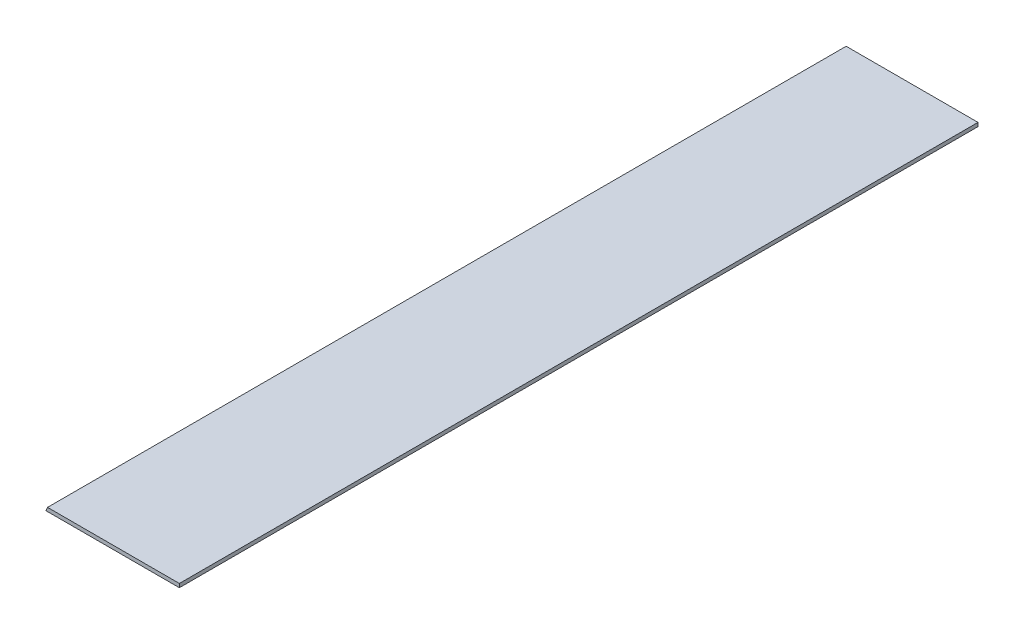
SolidWorks part; units mm, degrees
ref_plane "Front Plane" through (0, 0, 0) normal (0, 0, 1) x (1, 0, 0)
ref_plane "Top Plane" through (0, 0, 0) normal (0, 1, 0) x (1, 0, 0)
ref_plane "Right Plane" through (0, 0, 0) normal (1, 0, 0) x (0, 0, -1)
sketch "Sketch1" plane through (0, 0, 0) normal (0, 0, 1) x (1, 0, 0)
  line L0 (0, 0) -> (0.9785, 2.3622)
  line L1 (0.9785, 2.3622) -> (84.836, 2.3622)
  line L2 (84.836, 2.3622) -> (84.836, 0)
  line L3 (84.836, 0) -> (0, 0)
  dimension "D1" = 84.836
  dimension "D2" = 67.5
  dimension "D3" = 2.3622
extrude "Boss-Extrude1" add sketch "Sketch1" along normal blind 508
